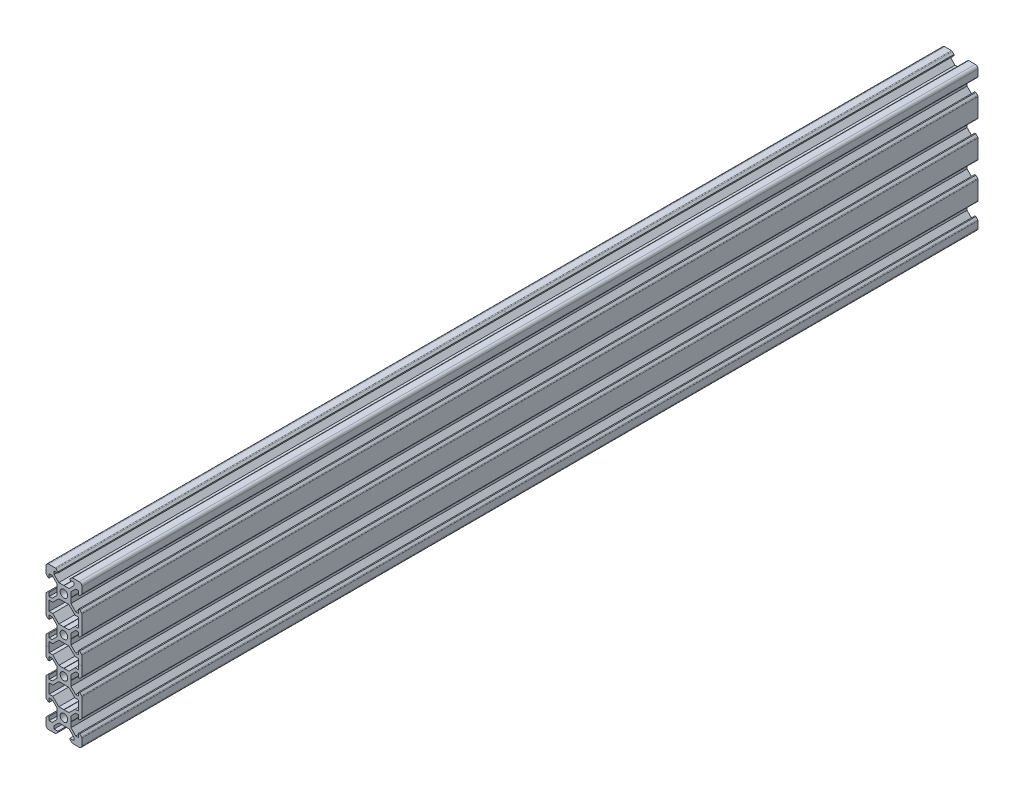
SolidWorks part; units mm, degrees
material "6063-T5"
ref_plane "Front" through (0, 0, 0) normal (0, 0, 1) x (1, 0, 0)
ref_plane "Top" through (0, 0, 0) normal (0, 1, 0) x (1, 0, 0)
ref_plane "Right" through (0, 0, 0) normal (1, 0, 0) x (0, 0, -1)
sketch "Sketch1" plane through (0, 0, 0) normal (0, 0, 1) x (1, 0, 0)
  line L0 (-8.5, 10) -> (-10, 8.5) construction
  line L1 (-8.5, 10) -> (-4.8628, 10)
  line L2 (-10, 8.5) -> (-10, 4.8628)
  line L3 (25.9287, -20) -> (-28.3599, -20) construction
  line L4 (10, 8.5) -> (10, 4.8628)
  line L5 (-10, 10) -> (10, -10) construction
  line L6 (-10, -10) -> (10, 10) construction
  line L7 (8.2, -5.5) -> (8.2, -3.3865)
  line L8 (-8.2, -5.5) -> (-8.2, -3.3865)
  line L9 (-5.5, 8.2) -> (-3.3865, 8.2)
  line L10 (-8.2, -12.7) -> (-8.2, -7.3)
  line L11 (-3.9005, 2.8395) -> (-6.561, 5.5)
  line L12 (-6.561, 5.5) -> (-8.2, 5.5)
  line L13 (-2.8395, -3.9005) -> (-0.1, -3.9005)
  line L14 (-3.9005, -2.8395) -> (-3.9005, -0.1)
  line L15 (-2.8395, 3.9005) -> (-0.1, 3.9005)
  line L16 (3.9005, -2.8395) -> (3.9005, -0.1)
  line L17 (-8.2, 3.3865) -> (-8.81, 3.3865)
  line L18 (-8.81, 3.3865) -> (-9.7976, 4.3741)
  line L19 (8.5, 10) -> (10, 8.5) construction
  line L20 (-2.8395, 3.9005) -> (-5.5, 6.561)
  line L21 (-5.5, 6.561) -> (-5.5, 8.2)
  line L22 (-3.3865, 8.2) -> (-3.3865, 8.81)
  line L23 (-3.3865, 8.81) -> (-4.3741, 9.7976)
  line L24 (0, 24.069) -> (0, -33.8154) construction
  line L25 (3.3865, 8.81) -> (4.3741, 9.7976)
  line L26 (3.3865, 8.2) -> (3.3865, 8.81)
  line L27 (5.5, 6.561) -> (5.5, 8.2)
  line L28 (2.8395, 3.9005) -> (5.5, 6.561)
  line L29 (3.3865, 8.2) -> (5.5, 8.2)
  line L30 (4.8628, 10) -> (8.5, 10)
  line L31 (-0.1, 3.9005) -> (0, 3.8005)
  line L32 (0.1, 3.9005) -> (0, 3.8005)
  line L33 (0.1, 3.9005) -> (2.8395, 3.9005)
  line L34 (25.9287, 0) -> (-28.3459, 0) construction
  line L35 (-0.1, -3.9005) -> (0, -3.8005)
  line L36 (0.1, -3.9005) -> (0, -3.8005)
  line L37 (0.1, -3.9005) -> (2.8395, -3.9005)
  line L38 (-3.9005, 0.1) -> (-3.8005, 0)
  line L39 (-3.8005, 0) -> (-3.9005, -0.1)
  line L40 (-3.9005, 0.1) -> (-3.9005, 2.8395)
  line L41 (3.9005, 0.1) -> (3.8005, 0)
  line L42 (3.8005, 0) -> (3.9005, -0.1)
  line L43 (3.9005, 0.1) -> (3.9005, 2.8395)
  line L44 (8.81, 3.3865) -> (9.7976, 4.3741)
  line L45 (8.2, 3.3865) -> (8.81, 3.3865)
  line L46 (6.561, 5.5) -> (8.2, 5.5)
  line L47 (3.9005, 2.8395) -> (6.561, 5.5)
  line L48 (2.8395, -3.9005) -> (5.5, -6.561)
  line L49 (3.9005, -2.8395) -> (6.561, -5.5)
  line L50 (-2.8395, -3.9005) -> (-5.5, -6.561)
  line L51 (-3.9005, -2.8395) -> (-6.561, -5.5)
  line L52 (6.561, -5.5) -> (8.2, -5.5)
  line L53 (-6.561, -5.5) -> (-8.2, -5.5)
  line L54 (-8.81, -3.3865) -> (-9.7976, -4.3741)
  line L55 (-8.2, -3.3865) -> (-8.81, -3.3865)
  line L56 (8.81, -3.3865) -> (9.7976, -4.3741)
  line L57 (8.2, -3.3865) -> (8.81, -3.3865)
  line L58 (8.2, 3.3865) -> (8.2, 5.5)
  line L59 (10, -4.8628) -> (10, -15.1372)
  line L60 (-8.2, 3.3865) -> (-8.2, 5.5)
  line L61 (-10, -4.8628) -> (-10, -15.1372)
  line L62 (-28.3459, -10) -> (-10, -10) construction
  line L63 (-3.9005, -20.1) -> (-3.9005, -22.8395)
  line L64 (-3.9005, -20.1) -> (-3.8005, -20)
  line L65 (-3.8005, -20) -> (-3.9005, -19.9)
  line L66 (3.9005, -20.1) -> (3.9005, -22.8395)
  line L67 (3.9005, -20.1) -> (3.8005, -20)
  line L68 (3.8005, -20) -> (3.9005, -19.9)
  line L69 (6.561, -14.5) -> (8.2, -14.5)
  line L70 (3.9005, -17.1605) -> (6.561, -14.5)
  line L71 (3.9005, -17.1605) -> (3.9005, -19.9)
  line L72 (-3.9005, -17.1605) -> (-3.9005, -19.9)
  line L73 (-3.9005, -17.1605) -> (-6.561, -14.5)
  line L74 (-6.561, -14.5) -> (-8.2, -14.5)
  line L75 (-8.2, -16.6135) -> (-8.81, -16.6135)
  line L76 (-8.81, -16.6135) -> (-9.7976, -15.6259)
  line L77 (8.2, -16.6135) -> (8.81, -16.6135)
  line L78 (8.81, -16.6135) -> (9.7976, -15.6259)
  line L79 (-2.8395, -16.0995) -> (-5.5, -13.439)
  line L80 (-2.8395, -16.0995) -> (-0.1, -16.0995)
  line L81 (-0.1, -16.0995) -> (0, -16.1995)
  line L82 (0.1, -16.0995) -> (0, -16.1995)
  line L83 (0.1, -16.0995) -> (2.8395, -16.0995)
  line L84 (2.8395, -16.0995) -> (5.5, -13.439)
  line L85 (-8.2, -16.6135) -> (-8.2, -14.5)
  line L86 (8.2, -16.6135) -> (8.2, -14.5)
  line L87 (2.8395, -23.9005) -> (5.5, -26.561)
  line L88 (-2.8395, -23.9005) -> (-5.5, -26.561)
  line L89 (-0.1, -23.9005) -> (0, -23.8005)
  line L90 (0.1, -23.9005) -> (0, -23.8005)
  line L91 (0.1, -23.9005) -> (2.8395, -23.9005)
  line L92 (-2.8395, -23.9005) -> (-0.1, -23.9005)
  line L93 (-8.2, -23.3865) -> (-8.2, -25.5)
  line L94 (-8.2, -23.3865) -> (-8.81, -23.3865)
  line L95 (-8.81, -23.3865) -> (-9.7976, -24.3741)
  line L96 (8.2, -23.3865) -> (8.2, -25.5)
  line L97 (8.2, -23.3865) -> (8.81, -23.3865)
  line L98 (8.81, -23.3865) -> (9.7976, -24.3741)
  line L99 (8.2, -27.3) -> (8.2, -32.7)
  line L100 (10, -35.1372) -> (10, -24.8628)
  line L101 (-10, -35.1372) -> (-10, -24.8628)
  line L102 (-8.2, -27.3) -> (-8.2, -32.7)
  line L103 (3.9005, -22.8395) -> (6.561, -25.5)
  line L104 (-3.9005, -22.8395) -> (-6.561, -25.5)
  line L105 (6.239, -27.3) -> (8.2, -27.3)
  line L106 (-6.239, -27.3) -> (-8.2, -27.3)
  line L107 (-6.561, -25.5) -> (-8.2, -25.5)
  line L108 (6.561, -25.5) -> (8.2, -25.5)
  line L109 (5.5, -26.561) -> (6.239, -27.3)
  line L110 (-5.5, -26.561) -> (-6.239, -27.3)
  line L111 (8.2, -34.5) -> (8.2, -36.6135)
  line L112 (8.2, -36.6135) -> (8.81, -36.6135)
  line L113 (8.81, -36.6135) -> (9.7976, -35.6259)
  line L114 (-8.2, -34.5) -> (-8.2, -36.6135)
  line L115 (-6.239, -7.3) -> (-8.2, -7.3)
  line L116 (-5.5, -6.561) -> (-6.239, -7.3)
  line L117 (6.239, -7.3) -> (8.2, -7.3)
  line L118 (5.5, -6.561) -> (6.239, -7.3)
  line L119 (-6.239, -12.7) -> (-8.2, -12.7)
  line L120 (-5.5, -13.439) -> (-6.239, -12.7)
  line L121 (5.5, -13.439) -> (6.239, -12.7)
  line L122 (6.239, -12.7) -> (8.2, -12.7)
  line L123 (8.2, -12.7) -> (8.2, -7.3)
  line L124 (-8.2, -36.6135) -> (-8.81, -36.6135)
  line L125 (10, -10) -> (25.9287, -10) construction
  line L126 (-8.81, -36.6135) -> (-9.7976, -35.6259)
  line L127 (-0.1, -56.0995) -> (0, -56.1995)
  line L128 (-0.1, -36.0995) -> (0, -36.1995)
  line L129 (0.1, -36.0995) -> (0, -36.1995)
  line L130 (0.1, -36.0995) -> (2.8395, -36.0995)
  line L131 (-6.561, -34.5) -> (-8.2, -34.5)
  line L132 (6.561, -34.5) -> (8.2, -34.5)
  line L133 (6.239, -32.7) -> (8.2, -32.7)
  line L134 (-6.239, -32.7) -> (-8.2, -32.7)
  line L135 (-5.5, -33.439) -> (-6.239, -32.7)
  line L136 (5.5, -33.439) -> (6.239, -32.7)
  line L137 (-26.6965, -30) -> (27.5921, -30) construction
  line L138 (0.1, -56.0995) -> (0, -56.1995)
  line L139 (0.1, -56.0995) -> (2.8395, -56.0995)
  line L140 (-2.8395, -56.0995) -> (-0.1, -56.0995)
  line L141 (0, -60) -> (0, -71.7864) construction
  line L142 (-3.8005, -60) -> (-3.9005, -59.9)
  line L143 (-3.9005, -60.1) -> (-3.8005, -60)
  line L144 (10, -68.5) -> (10, -64.8628)
  line L145 (0.1, -63.9005) -> (0, -63.8005)
  line L146 (-0.1, -63.9005) -> (0, -63.8005)
  line L147 (-2.8395, -63.9005) -> (-0.1, -63.9005)
  line L148 (0.1, -63.9005) -> (2.8395, -63.9005)
  line L149 (3.9005, -60.1) -> (3.9005, -62.8395)
  line L150 (3.9005, -60.1) -> (3.8005, -60)
  line L151 (3.8005, -60) -> (3.9005, -59.9)
  line L152 (3.9005, -57.1605) -> (3.9005, -59.9)
  line L153 (4.8628, -70) -> (8.5, -70)
  line L154 (3.3865, -68.81) -> (4.3741, -69.7976)
  line L155 (3.3865, -68.2) -> (3.3865, -68.81)
  line L156 (3.3865, -68.2) -> (5.5, -68.2)
  line L157 (-0.1, -43.9005) -> (0, -43.8005)
  line L158 (0.1, -43.9005) -> (0, -43.8005)
  line L159 (-2.8395, -43.9005) -> (-0.1, -43.9005)
  line L160 (0.1, -43.9005) -> (2.8395, -43.9005)
  line L161 (3.9005, -40.1) -> (3.8005, -40)
  line L162 (3.8005, -40) -> (3.9005, -39.9)
  line L163 (3.9005, -37.1605) -> (3.9005, -39.9)
  line L164 (3.9005, -40.1) -> (3.9005, -42.8395)
  line L165 (-2.8395, -36.0995) -> (-0.1, -36.0995)
  line L166 (-2.8395, -43.9005) -> (-5.5, -46.561)
  line L167 (-3.9005, -37.1605) -> (-3.9005, -39.9)
  line L168 (-3.8005, -40) -> (-3.9005, -39.9)
  line L169 (-3.9005, -40.1) -> (-3.8005, -40)
  line L170 (-3.9005, -42.8395) -> (-6.561, -45.5)
  line L171 (2.8395, -43.9005) -> (5.5, -46.561)
  line L172 (3.9005, -42.8395) -> (6.561, -45.5)
  line L173 (3.9005, -37.1605) -> (6.561, -34.5)
  line L174 (2.8395, -36.0995) -> (5.5, -33.439)
  line L175 (-3.9005, -42.8395) -> (-3.9005, -40.1)
  line L176 (-6.561, -34.5) -> (-3.9005, -37.1605)
  line L177 (-5.5, -33.439) -> (-2.8395, -36.0995)
  line L178 (5.5, -66.561) -> (5.5, -68.2)
  line L179 (6.561, -65.5) -> (8.2, -65.5)
  line L180 (8.2, -63.3865) -> (8.2, -65.5)
  line L181 (8.81, -63.3865) -> (9.7976, -64.3741)
  line L182 (8.2, -63.3865) -> (8.81, -63.3865)
  line L183 (-8.2, -63.3865) -> (-8.81, -63.3865)
  line L184 (-8.81, -63.3865) -> (-9.7976, -64.3741)
  line L185 (-8.2, -63.3865) -> (-8.2, -65.5)
  line L186 (-6.561, -65.5) -> (-8.2, -65.5)
  line L187 (-5.5, -66.561) -> (-5.5, -68.2)
  line L188 (-5.5, -68.2) -> (-3.3865, -68.2)
  line L189 (-3.3865, -68.2) -> (-3.3865, -68.81)
  line L190 (-3.3865, -68.81) -> (-4.3741, -69.7976)
  line L191 (-10, -68.5) -> (-10, -64.8628)
  line L192 (-8.5, -70) -> (-4.8628, -70)
  line L193 (-8.2, -43.3865) -> (-8.81, -43.3865)
  line L194 (-8.81, -43.3865) -> (-9.7976, -44.3741)
  line L195 (-10, -55.1372) -> (-10, -44.8628)
  line L196 (-8.81, -56.6135) -> (-9.7976, -55.6259)
  line L197 (-8.2, -56.6135) -> (-8.81, -56.6135)
  line L198 (8.2, -56.6135) -> (8.81, -56.6135)
  line L199 (8.81, -56.6135) -> (9.7976, -55.6259)
  line L200 (8.2, -43.3865) -> (8.81, -43.3865)
  line L201 (8.81, -43.3865) -> (9.7976, -44.3741)
  line L202 (10, -55.1372) -> (10, -44.8628)
  line L203 (-8.2, -47.3) -> (-8.2, -52.7)
  line L204 (8.2, -47.3) -> (8.2, -52.7)
  line L205 (-6.239, -52.7) -> (-8.2, -52.7)
  line L206 (6.239, -52.7) -> (8.2, -52.7)
  line L207 (-6.561, -54.5) -> (-8.2, -54.5)
  line L208 (6.561, -54.5) -> (8.2, -54.5)
  line L209 (-3.9005, -60.1) -> (-3.9005, -62.8395)
  line L210 (-2.8395, -56.0995) -> (-5.5, -53.439)
  line L211 (3.9005, -57.1605) -> (6.561, -54.5)
  line L212 (2.8395, -56.0995) -> (5.5, -53.439)
  line L213 (5.5, -53.439) -> (6.239, -52.7)
  line L214 (-5.5, -53.439) -> (-6.239, -52.7)
  line L215 (-8.2, -43.3865) -> (-8.2, -45.5)
  line L216 (8.2, -43.3865) -> (8.2, -45.5)
  line L217 (-2.8395, -63.9005) -> (-5.5, -66.561)
  line L218 (-3.9005, -62.8395) -> (-6.561, -65.5)
  line L219 (2.8395, -63.9005) -> (5.5, -66.561)
  line L220 (3.9005, -62.8395) -> (6.561, -65.5)
  line L221 (-8.2, -54.5) -> (-8.2, -56.6135)
  line L222 (8.2, -54.5) -> (8.2, -56.6135)
  line L223 (6.239, -47.3) -> (8.2, -47.3)
  line L224 (-6.239, -47.3) -> (-8.2, -47.3)
  line L225 (-6.561, -45.5) -> (-8.2, -45.5)
  line L226 (-5.5, -46.561) -> (-6.239, -47.3)
  line L227 (6.561, -45.5) -> (8.2, -45.5)
  line L228 (5.5, -46.561) -> (6.239, -47.3)
  line L229 (-3.9005, -57.1605) -> (-3.9005, -59.9)
  line L230 (-3.9005, -57.1605) -> (-6.561, -54.5)
  circle A0 centre (0, 0) radius 2.1
  arc A1 (-8.5, 10) -> (-10, 8.5) centre (-8.5, 8.5) ccw
  arc A2 (10, 8.5) -> (8.5, 10) centre (8.5, 8.5) ccw
  arc A3 (-4.3741, 9.7976) -> (-4.8628, 10) centre (-4.8628, 9.3088) ccw
  arc A4 (4.8628, 10) -> (4.3741, 9.7976) centre (4.8628, 9.3088) ccw
  circle A5 centre (0, -20) radius 2.1
  arc A6 (9.7976, 4.3741) -> (10, 4.8628) centre (9.3088, 4.8628) ccw
  arc A7 (-10, 4.8628) -> (-9.7976, 4.3741) centre (-9.3088, 4.8628) ccw
  arc A8 (-10, -4.8628) -> (-9.7976, -4.3741) centre (-9.3088, -4.8628) cw
  arc A9 (9.7976, -4.3741) -> (10, -4.8628) centre (9.3088, -4.8628) cw
  arc A10 (-10, -15.1372) -> (-9.7976, -15.6259) centre (-9.3088, -15.1372) ccw
  arc A11 (9.7976, -15.6259) -> (10, -15.1372) centre (9.3088, -15.1372) ccw
  arc A12 (-10, -24.8628) -> (-9.7976, -24.3741) centre (-9.3088, -24.8628) cw
  arc A13 (9.7976, -24.3741) -> (10, -24.8628) centre (9.3088, -24.8628) cw
  arc A14 (9.7976, -35.6259) -> (10, -35.1372) centre (9.3088, -35.1372) ccw
  arc A15 (-10, -35.1372) -> (-9.7976, -35.6259) centre (-9.3088, -35.1372) ccw
  circle A16 centre (0, -40) radius 2.1
  circle A17 centre (0, -60) radius 2.1
  arc A18 (10, -68.5) -> (8.5, -70) centre (8.5, -68.5) cw
  arc A19 (4.8628, -70) -> (4.3741, -69.7976) centre (4.8628, -69.3088) cw
  arc A20 (9.7976, -64.3741) -> (10, -64.8628) centre (9.3088, -64.8628) cw
  arc A21 (-10, -64.8628) -> (-9.7976, -64.3741) centre (-9.3088, -64.8628) cw
  arc A22 (-4.3741, -69.7976) -> (-4.8628, -70) centre (-4.8628, -69.3088) cw
  arc A23 (-8.5, -70) -> (-10, -68.5) centre (-8.5, -68.5) cw
  arc A24 (-10, -44.8628) -> (-9.7976, -44.3741) centre (-9.3088, -44.8628) cw
  arc A25 (-10, -55.1372) -> (-9.7976, -55.6259) centre (-9.3088, -55.1372) ccw
  arc A26 (9.7976, -55.6259) -> (10, -55.1372) centre (9.3088, -55.1372) ccw
  arc A27 (9.7976, -44.3741) -> (10, -44.8628) centre (9.3088, -44.8628) cw
  point P17 (-9.25, 9.25)
  point P21 (9.25, 9.25)
  point P181 (-10, -30)
  dimension "D2" = 4.2
  dimension "D4" = 1.5
  dimension "D3" = 20
  dimension "D5" = 0.529
  dimension "D6" = 6.773
  dimension "D7" = 90
  dimension "D8" = 11
  dimension "D9" = 0.61
  dimension "D10" = 0.1
  dimension "D11" = 0.1
  dimension "D12" = 0.1
  dimension "D13" = 0.1
  dimension "D14" = 5.679
  dimension "D15" = 1.639
  dimension "D16" = 1.8
  dimension "D17" = 90
  dimension "D18" = 6.773
  dimension "D19" = 90
  dimension "D20" = 20
  dimension "D21" = 1.8
extrude "Boss-Extrude2" add sketch "Sketch1" along normal blind 500
sketch "Sketch2" plane through (0, 0, 500) normal (0, 0, 1) x (1, 0, 0)
  line L0 (-10, -30) -> (10, -30)
  line L1 (-10, -24.8628) -> (-10, -35.1372) construction
  line L2 (10, -35.1372) -> (10, -24.8628) construction
split line "SideFixture1 - SplitLine"
sketch "Sketch3" plane through (0, 0, 0) normal (0, 0, -1) x (-1, 0, 0)
  line L0 (-10, -30) -> (10, -30)
  line L1 (-10, -35.1372) -> (-10, -24.8628) construction
  line L2 (10, -24.8628) -> (10, -35.1372) construction
split line "SideFixture2 - SplitLine"
sketch "Sketch4" plane through (0, 10, 0) normal (0, 1, 0) x (1, 0, 0)
  line L0 (8.5, -250) -> (-8.5, -250)
  line L1 (8.5, -500) -> (8.5, 0) construction
  line L2 (-8.5, -500) -> (-8.5, 0) construction
split line "SideFixture3 - SplitLine"
